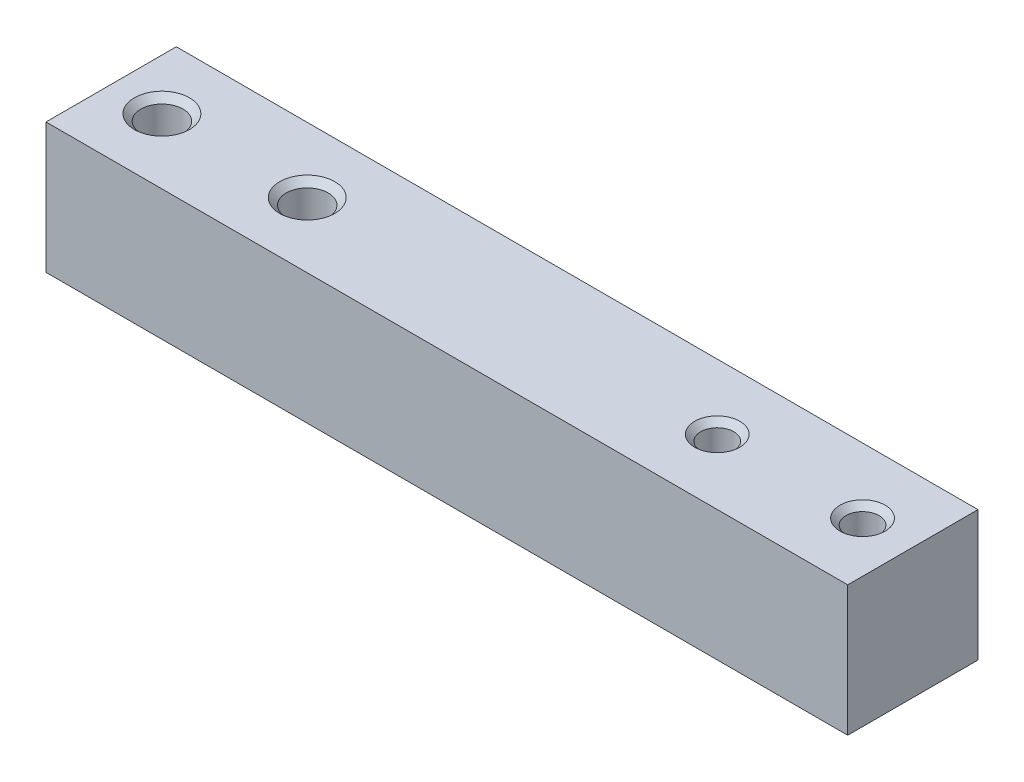
SolidWorks part; units mm, degrees
ref_plane "Front Plane" through (0, 0, 0) normal (0, 0, 1) x (1, 0, 0)
ref_plane "Top Plane" through (0, 0, 0) normal (0, 1, 0) x (1, 0, 0)
ref_plane "Right Plane" through (0, 0, 0) normal (1, 0, 0) x (0, 0, -1)
sketch "Sketch1" plane through (0, 0, 0) normal (0, 1, 0) x (1, 0, 0)
  line L1 (0, 0) -> (80, 0)
  line L2 (0, 0) -> (0, 13)
  line L3 (0, 13) -> (80, 13)
  line L4 (80, 0) -> (80, 13)
  dimension "D1" = 13
  dimension "D2" = 80
extrude "Boss-Extrude1" add sketch "Sketch1" along normal blind 13
sketch "Sketch2" plane through (0, 13, 0) normal (0, 1, 0) x (1, 0, 0)
  line L0 (0, 6.5) -> (80, 6.5) construction
  line L1 (0, 13) -> (0, 0) construction
  line L2 (80, 0) -> (80, 13) construction
  point P6 (74.979, 6.5)
  point P7 (60.479, 6.5)
  point P8 (19.567, 6.5)
  point P9 (5.067, 6.5)
  dimension "D1" = 5.021
  dimension "D2" = 14.5
  dimension "D3" = 5.067
  dimension "D4" = 14.5
hole_wizard "M4x0.7 Tapped Hole1" positions "3DSketch1" profile "Sketch3" tap size "M4x0.7" standard "ANSI Metric" end condition through all
sketch3d "3DSketch1"
  point P0 (74.979, 13, -6.5)
  point P3 (60.479, 13, -6.5)
sketch "Sketch3" plane through (74.979, 13, -6.5) normal (1, 0, 0) x (0, 0, 1)
  line L0 (0, 0) -> (0, 13)
  line L1 (0, 13) -> (1.65, 13)
  line L2 (1.65, 13) -> (1.65, 0.6)
  line L3 (1.65, 0.6) -> (2.25, 0)
  line L5 (2.25, 0) -> (0, 0)
  line L6 (-1.65, 0.6) -> (-2.25, 0) construction
  line L11 (0, -6.35) -> (0, 107.95) construction
  dimension "Thread Major Dia." = 3.3
  dimension "Thru Tap Drill Depth" = 13
  dimension "Near C'Sink Dia." = 4.5
  dimension "Near C'Sink Angle" = 90
hole_wizard "M5x0.8 Tapped Hole1" positions "3DSketch2" profile "Sketch4" tap size "M5x0.8" standard "ANSI Metric" end condition through all
sketch3d "3DSketch2"
  point P0 (5.067, 13, -6.5)
  point P3 (19.567, 13, -6.5)
sketch "Sketch4" plane through (5.067, 13, -6.5) normal (1, 0, 0) x (0, 0, 1)
  line L0 (0, 0) -> (0, 13)
  line L1 (0, 13) -> (2.1, 13)
  line L2 (2.1, 13) -> (2.1, 0.65)
  line L3 (2.1, 0.65) -> (2.75, 0)
  line L5 (2.75, 0) -> (0, 0)
  line L6 (-2.1, 0.65) -> (-2.75, 0) construction
  line L11 (0, -6.35) -> (0, 107.95) construction
  dimension "Thread Major Dia." = 4.2
  dimension "Thru Tap Drill Depth" = 13
  dimension "Near C'Sink Dia." = 5.5
  dimension "Near C'Sink Angle" = 90
fillet "Fillet1" [suppressed] radius 0.25
